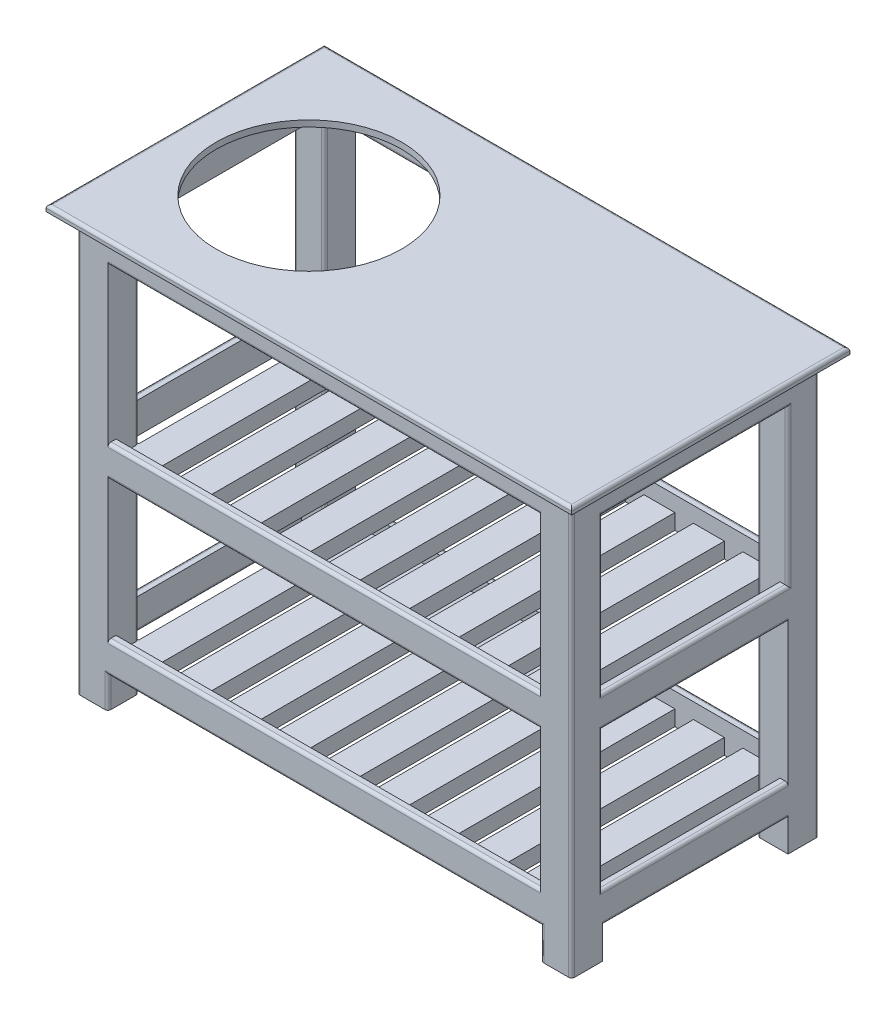
SolidWorks part; units mm, degrees
ref_plane "Front Plane" through (0, 0, 0) normal (0, 0, 1) x (1, 0, 0)
ref_plane "Top Plane" through (0, 0, 0) normal (0, 1, 0) x (1, 0, 0)
ref_plane "Right Plane" through (0, 0, 0) normal (1, 0, 0) x (0, 0, -1)
sketch "Sketch1" plane through (0, 0, 0) normal (0, 1, 0) x (1, 0, 0)
  line L1 (-425, -225) -> (425, -225)
  line L2 (-425, -225) -> (-425, 225)
  line L3 (-425, 225) -> (425, 225)
  line L4 (425, -225) -> (425, 225)
  line L5 (-425, -225) -> (425, 225) construction
  line L6 (-425, 225) -> (425, -225) construction
  point P0 (0, 0)
  dimension "D1" = 850
  dimension "D2" = 450
extrude "Boss-Extrude1" add sketch "Sketch1" along normal blind 10
sketch "Sketch2" plane through (0, 0, 0) normal (0, -1, 0) x (1, 0, 0)
  line L0 (-400, 225) -> (-400, -225) construction
  line L17 (-425, 225) -> (425, 225) construction
  line L18 (425, -225) -> (-425, -225) construction
  line L19 (400, 225) -> (400, -225) construction
  line L20 (-400, -200) -> (400, -200) construction
  line L21 (-400, 200) -> (400, 200) construction
  line L22 (-425, -225) -> (-425, 225) construction
  line L23 (425, 225) -> (425, -225) construction
  line L25 (-400, -200) -> (-350, -200)
  line L26 (-400, -200) -> (-400, -150)
  line L27 (-400, -150) -> (-350, -150)
  line L28 (-350, -200) -> (-350, -150)
  line L29 (-400, 200) -> (-350, 200)
  line L30 (-400, 200) -> (-400, 150)
  line L31 (-400, 150) -> (-350, 150)
  line L32 (-350, 200) -> (-350, 150)
  line L33 (400, 200) -> (350, 200)
  line L34 (400, 200) -> (400, 150)
  line L35 (400, 150) -> (350, 150)
  line L36 (350, 200) -> (350, 150)
  line L37 (400, -200) -> (350, -200)
  line L38 (400, -200) -> (400, -150)
  line L39 (400, -150) -> (350, -150)
  line L40 (350, -200) -> (350, -150)
  dimension "D1" = 25
  dimension "D2" = 25
  dimension "D3" = 25
  dimension "D4" = 25
  dimension "D5" = 50
extrude "Boss-Extrude2" add sketch "Sketch2" along normal blind 675
sketch "Sketch3" plane through (-350, 0, 0) normal (1, 0, 0) x (0, 0, -1)
  line L0 (200, -675) -> (150, -675) construction
  line L1 (187, -575) -> (200, -575)
  line L2 (187, -575) -> (187, -625)
  line L3 (187, -625) -> (200, -625)
  line L4 (200, -575) -> (200, -625)
  line L5 (187, -575) -> (200, -625) construction
  line L6 (187, -625) -> (200, -575) construction
  line L7 (187, -350) -> (200, -350)
  line L8 (187, -350) -> (187, -300)
  line L9 (187, -300) -> (200, -300)
  line L10 (200, -350) -> (200, -300)
  line L11 (187, -350) -> (200, -300) construction
  line L12 (187, -300) -> (200, -350) construction
  line L13 (200, -50) -> (187, -50)
  line L14 (200, -50) -> (200, 0)
  line L15 (200, 0) -> (187, 0)
  line L16 (187, -50) -> (187, 0)
  line L18 (200, 0) -> (150, 0) construction
  line L19 (200, -675) -> (200, 0) construction
  point P0 (193.5, -600)
  point P5 (193.5, -325)
  dimension "D1" = 13
  dimension "D2" = 50
  dimension "D3" = 50
  dimension "D6" = 325
  dimension "D7" = 50
  dimension "D8" = 13
  dimension "D10" = 13
  dimension "D11" = 50
extrude "Boss-Extrude3" add sketch "Sketch3" along normal up to next
mirror "Mirror1" about plane through (0, 0, 0) normal (0, 0, 1) of bodies 103
sketch "Sketch4" plane through (0, 0, -150) normal (0, 0, 1) x (1, 0, 0)
  line L0 (400, -675) -> (400, 0) construction
  line L1 (400, -575) -> (387, -575)
  line L2 (400, -575) -> (400, -625)
  line L3 (400, -625) -> (387, -625)
  line L4 (387, -575) -> (387, -625)
  line L5 (350, -575) -> (-350, -575) construction
  line L6 (350, -300) -> (-350, -300) construction
  line L7 (400, -300) -> (387, -300)
  line L8 (400, -300) -> (400, -350)
  line L9 (400, -350) -> (387, -350)
  line L10 (387, -300) -> (387, -350)
  line L11 (400, 0) -> (387, 0)
  line L12 (400, 0) -> (400, -50)
  line L13 (400, -50) -> (387, -50)
  line L14 (387, 0) -> (387, -50)
  dimension "D1" = 50
  dimension "D2" = 13
  dimension "D3" = 13
  dimension "D4" = 13
  dimension "D5" = 50
  dimension "D6" = 50
extrude "Boss-Extrude4" add sketch "Sketch4" along normal up to next
mirror "Mirror2" about plane through (0, 0, 0) normal (1, 0, 0) of bodies 105
sketch "Sketch5" plane through (0, 0, -187) normal (0, 0, 1) x (1, 0, 0)
  line L1 (-350, -350) -> (-300, -350)
  line L2 (-350, -350) -> (-350, -325)
  line L3 (-350, -325) -> (-300, -325)
  line L4 (-300, -350) -> (-300, -325)
  dimension "D1" = 25
  dimension "D2" = 50
extrude "Boss-Extrude5" add sketch "Sketch5" along normal up to next (374 mm away)
sketch "Sketch6" plane through (0, 0, -187) normal (0, 0, 1) x (1, 0, 0)
  line L1 (-350, -625) -> (-300, -625)
  line L2 (-350, -625) -> (-350, -600)
  line L3 (-350, -600) -> (-300, -600)
  line L4 (-300, -625) -> (-300, -600)
  dimension "D1" = 25
  dimension "D2" = 50
extrude "Boss-Extrude6" add sketch "Sketch6" along normal up to next (374 mm away)
pattern_linear "LPattern2" count 9 spacing 80 along (1, 0, 0) of "Boss-Extrude5"
pattern_linear "LPattern3" count 9 spacing 80 along (1, 0, 0) of "Boss-Extrude6"
sketch "Sketch7" plane through (0, 10, 0) normal (0, 1, 0) x (1, 0, 0)
  line L0 (-425, 0) -> (425, 0) construction
  line L1 (-425, 225) -> (-425, -225) construction
  line L2 (425, -225) -> (425, 225) construction
  line L3 (-225, 225) -> (-225, -173.2947) construction
  line L4 (425, 225) -> (-425, 225) construction
  circle A1 centre (-225, 0) radius 150
  dimension "D1" = 200
  dimension "D2" = 300
extrude "Cut-Extrude1" cut sketch "Sketch7" against normal up to next
fillet "Fillet2" radius 5 37 edges at (0, -300, 200) (0, -575, 200) (0, -625, 200) (0, -350, 200) (0, -50, 200) (-400, -650, -150) (-400, -337.5, -200) (-350, -650, -150) (400, -575, 0) (400, -625, 0) (400, -300, 0) (400, -350, 0) (400, -50, 0) (400, -337.5, -200) (350, -337.5, -150) (-400, -462.5, 150) (-400, -175, 150) (-400, -462.5, -150) (-400, -175, -150) (-400, -300, 0) (-400, -575, 0) (-387, -625, 0) (-400, -350, 0) (-400, -50, 0) (-400, -337.5, 200) (-350, -650, 150) (-350, -162.5, -150) (-350, -162.5, 150) (-350, -475, 150) (-350, -475, -150) (400, -337.5, 200) (350, -337.5, 150) (0, -575, -200) (0, -625, -200) (0, -300, -200) (0, -350, -200) (0, -50, -187)
fillet "Fillet3" radius 5 4 edges at (425, 10, 0) (0, 10, -225) (-425, 10, 0) (0, 10, 225)
